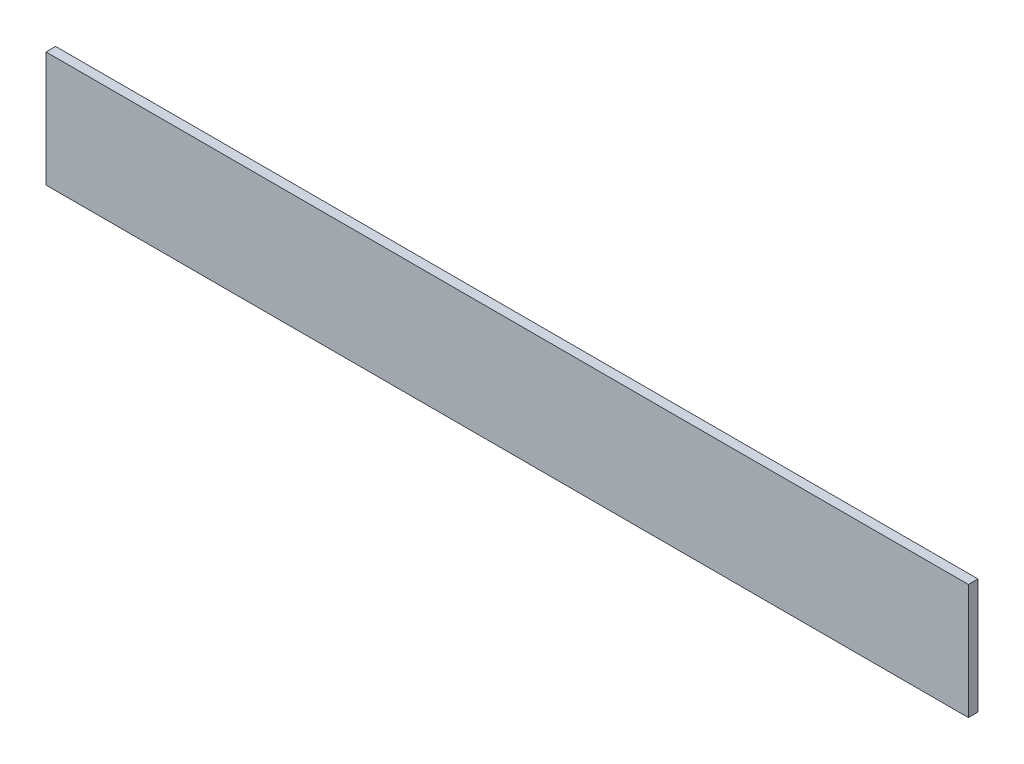
SolidWorks part; units mm, degrees
ref_plane "Front Plane" through (0, 0, 0) normal (0, 0, 1) x (1, 0, 0)
ref_plane "Top Plane" through (0, 0, 0) normal (0, 1, 0) x (1, 0, 0)
ref_plane "Right Plane" through (0, 0, 0) normal (1, 0, 0) x (0, 0, -1)
sketch "Sketch1" plane through (0, 0, 0) normal (0, 0, 1) x (1, 0, 0)
  line L1 (-304.8, -38.1) -> (304.8, -38.1)
  line L2 (-304.8, -38.1) -> (-304.8, 38.1)
  line L3 (-304.8, 38.1) -> (304.8, 38.1)
  line L4 (304.8, -38.1) -> (304.8, 38.1)
  line L5 (-304.8, -38.1) -> (304.8, 38.1) construction
  line L6 (-304.8, 38.1) -> (304.8, -38.1) construction
  point P0 (0, 0)
  dimension "D1" = 609.6
  dimension "D2" = 76.2
extrude "Boss-Extrude1" add sketch "Sketch1" along normal blind 6.35
